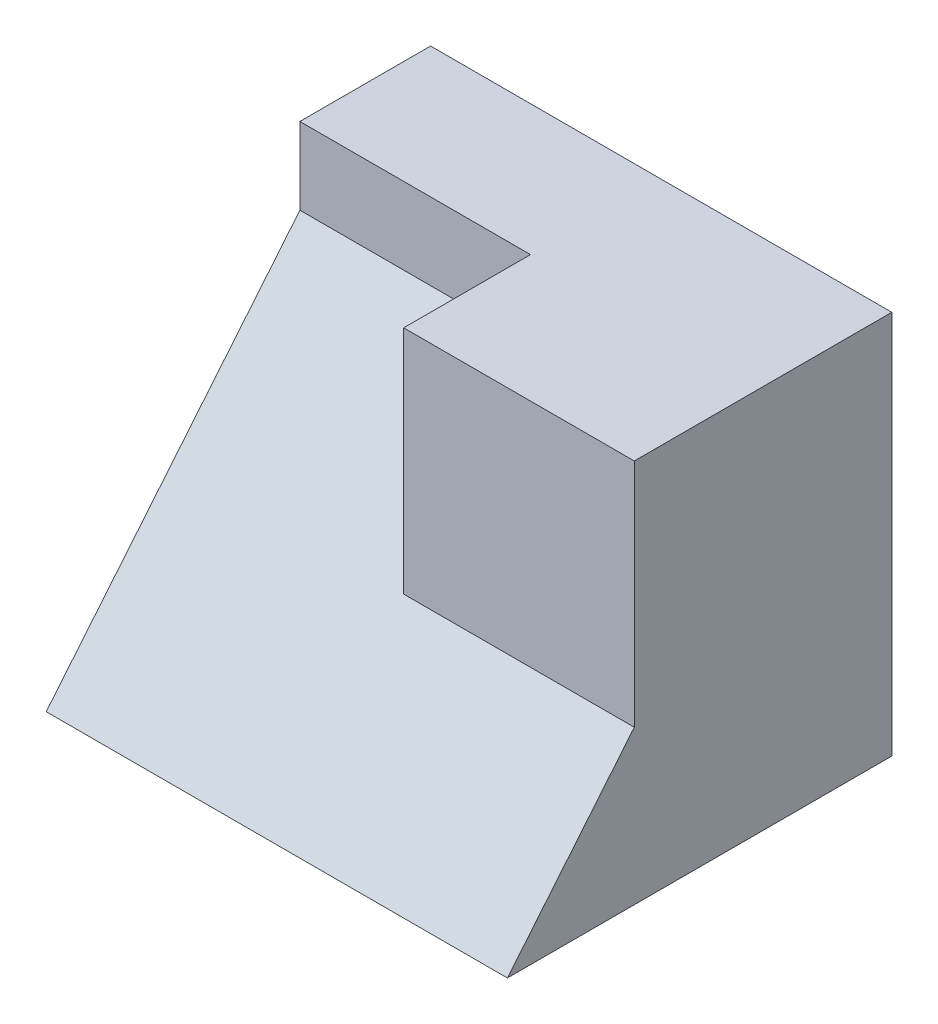
SolidWorks part; units mm, degrees
ref_plane "Front Plane" through (0, 0, 0) normal (0, 0, 1) x (1, 0, 0)
ref_plane "Top Plane" through (0, 0, 0) normal (0, 1, 0) x (1, 0, 0)
ref_plane "Right Plane" through (0, 0, 0) normal (1, 0, 0) x (0, 0, -1)
sketch "Sketch1" plane through (0, 0, 0) normal (0, 0, 1) x (1, 0, 0)
  line L1 (0, 0) -> (60, 0)
  line L2 (0, 0) -> (0, 50)
  line L3 (0, 50) -> (60, 50)
  line L4 (60, 0) -> (60, 50)
  dimension "D1" = 60
  dimension "D2" = 50
extrude "Boss-Extrude1" add sketch "Sketch1" along normal blind 50
sketch "Sketch2" plane through (0, 0, 50) normal (0, 0, 1) x (1, 0, 0)
  line L1 (0, 50) -> (30, 50)
  line L2 (0, 50) -> (0, 40)
  line L3 (0, 40) -> (30, 40)
  line L4 (30, 50) -> (30, 40)
  dimension "D1" = 30
  dimension "D2" = 10
extrude "Cut-Extrude1" cut sketch "Sketch2" against normal blind 40
sketch "Sketch3" plane through (0, 0, 50) normal (0, 0, 1) x (1, 0, 0)
  line L1 (60, 50) -> (30, 50)
  line L2 (60, 50) -> (60, 20)
  line L3 (60, 20) -> (30, 20)
  line L4 (30, 50) -> (30, 20)
  dimension "D1" = 30
  dimension "D2" = 30
extrude "Cut-Extrude2" cut sketch "Sketch3" against normal blind 30
sketch "Sketch4" plane through (0, 0, 10) normal (0, 0, 1) x (1, 0, 0)
  line L1 (0, 50) -> (30, 50)
  line L2 (0, 50) -> (0, 40)
  line L3 (0, 40) -> (30, 40)
  line L4 (30, 50) -> (30, 40)
  dimension "D1" = 30
  dimension "D2" = 10
extrude "Boss-Extrude2" add sketch "Sketch4" along normal blind 7
sketch "Sketch5" plane through (0, 0, 20) normal (0, 0, 1) x (1, 0, 0)
  line L1 (30, 20) -> (60, 20)
  line L2 (30, 20) -> (30, 50)
  line L3 (30, 50) -> (60, 50)
  line L4 (60, 20) -> (60, 50)
extrude "Boss-Extrude3" add sketch "Sketch5" along normal blind 12
sketch "Sketch10" plane through (0, 0, 0) normal (1, 0, 0) x (0, 0, -1)
  line L0 (-17, 40) -> (-50, 0)
  line L1 (-50, 0) -> (-50, 40)
  line L2 (-50, 40) -> (-17, 40)
extrude "Cut-Extrude6" cut sketch "Sketch10" along normal blind 10
sketch "Sketch11" plane through (10, 0, 0) normal (-1, 0, 0) x (0, 0, 1)
  line L0 (17, 40) -> (50, 40)
  line L1 (50, 40) -> (50, 0)
  line L2 (50, 0) -> (17, 40)
extrude "Cut-Extrude7" cut sketch "Sketch11" against normal blind 20
sketch "Sketch12" plane through (30, 0, 0) normal (-1, 0, 0) x (0, 0, 1)
  line L0 (33.5, 20) -> (50, 0)
  line L1 (50, 0) -> (50, 20)
  line L2 (50, 20) -> (33.5, 20)
extrude "Cut-Extrude8" cut sketch "Sketch12" against normal blind 52
sketch "Sketch13" plane through (0, 0, 32) normal (0, 0, 1) x (1, 0, 0)
  line L1 (30, 50) -> (60, 50)
  line L2 (30, 50) -> (30, 20)
  line L3 (30, 20) -> (60, 20)
  line L4 (60, 50) -> (60, 20)
extrude "Boss-Extrude4" add sketch "Sketch13" along normal blind 1.5
